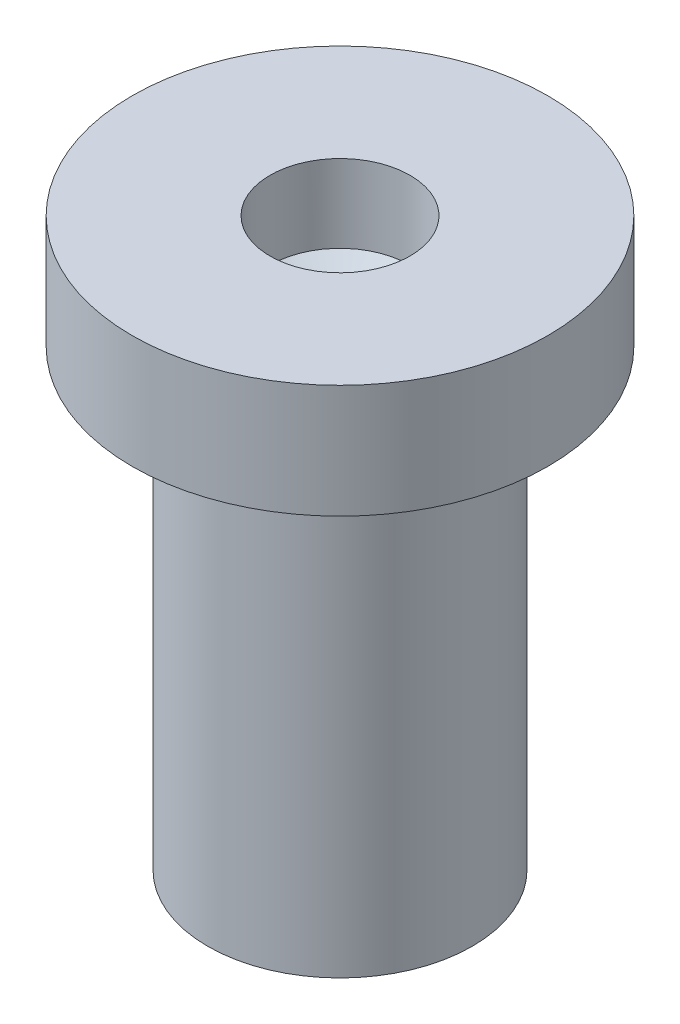
SolidWorks part; units mm, degrees
ref_plane "Front Plane" through (0, 0, 0) normal (0, 0, 1) x (1, 0, 0)
ref_plane "Top Plane" through (0, 0, 0) normal (0, 1, 0) x (1, 0, 0)
ref_plane "Right Plane" through (0, 0, 0) normal (1, 0, 0) x (0, 0, -1)
sketch "Sketch1" plane through (0, 0, 0) normal (0, 0, 1) x (1, 0, 0)
  line L0 (1.75, 0) -> (0, 0)
  line L2 (1.75, 0) -> (1.75, 6)
  line L3 (1.75, 6) -> (2.75, 6)
  line L4 (2.75, 6) -> (2.75, 7.5)
  line L5 (2.75, 7.5) -> (0.9266, 7.5)
  line L9 (0, 0) -> (0, 8.1432) construction
  line L10 (0.9266, 7.5) -> (0.9266, 6.4705)
  line L11 (0.9266, 6.4705) -> (0, 6)
  line L12 (0, 6) -> (0, 0)
  point P10 (0, 6.1453)
  point P11 (0.8082, 6.429)
  point P13 (0, 6)
  dimension "D1" = 1
  dimension "D2" = 6
  dimension "D3" = 1.5
revolve "Revolve1" add sketch "Sketch1" angle 360 about L9
